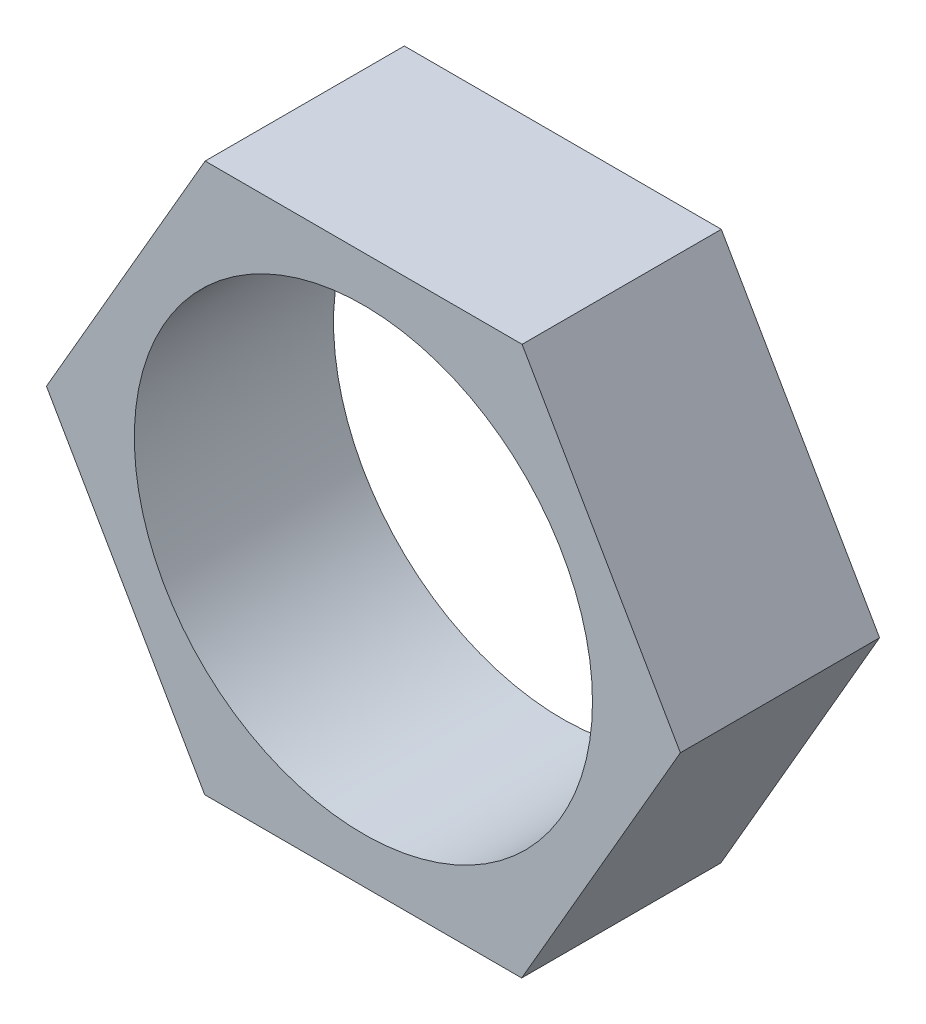
SolidWorks part; units mm, degrees
ref_plane "Alzado" through (0, 0, 0) normal (0, 0, 1) x (1, 0, 0)
ref_plane "Planta" through (0, 0, 0) normal (0, 1, 0) x (1, 0, 0)
ref_plane "Vista lateral" through (0, 0, 0) normal (1, 0, 0) x (0, 0, -1)
sketch "Croquis1" plane through (0, 0, 0) normal (0, 0, 1) x (1, 0, 0)
  line L1 (7.967, 13.7742) -> (-7.9453, 13.7867)
  line L2 (-7.9453, 13.7867) -> (-15.9123, 0.0125)
  line L3 (-15.9123, 0.0125) -> (-7.967, -13.7742)
  line L4 (-7.967, -13.7742) -> (7.9453, -13.7867)
  line L5 (7.9453, -13.7867) -> (15.9123, -0.0125)
  line L6 (15.9123, -0.0125) -> (7.967, 13.7742)
  circle A0 centre (0, 0) radius 11.5
  circle A1 centre (0, 0) radius 13.7805 construction
  dimension "D1" = 23
extrude "Saliente-Extruir1" add sketch "Croquis1" along normal blind 10
